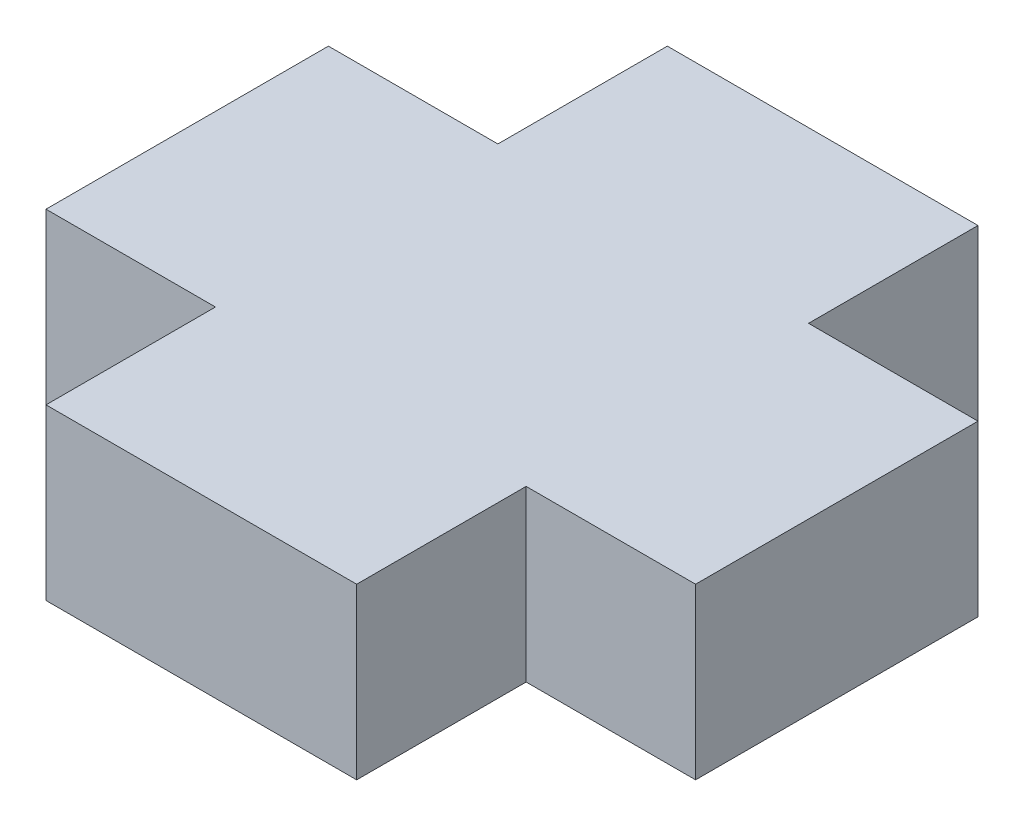
SolidWorks part; units mm, degrees
ref_plane "Front Plane" through (0, 0, 0) normal (0, 0, 1) x (1, 0, 0)
ref_plane "Top Plane" through (0, 0, 0) normal (0, 1, 0) x (1, 0, 0)
ref_plane "Right Plane" through (0, 0, 0) normal (1, 0, 0) x (0, 0, -1)
sketch "Sketch1" plane through (0, 0, 0) normal (0, 1, 0) x (1, 0, 0)
  line L0 (-16.2201, -4.3447) -> (-16.2201, 0.6553)
  line L1 (-16.2201, 0.6553) -> (-13.2201, 0.6553)
  line L2 (-13.2201, 0.6553) -> (-13.2201, 3.6553)
  line L3 (-13.2201, 3.6553) -> (-7.7201, 3.6553)
  line L4 (-7.7201, 3.6553) -> (-7.7201, 0.6553)
  line L5 (-7.7201, 0.6553) -> (-4.7201, 0.6553)
  line L6 (-4.7201, 0.6553) -> (-4.7201, -4.3447)
  line L7 (-4.7201, -4.3447) -> (-7.7201, -4.3447)
  line L8 (-7.7201, -4.3447) -> (-7.7201, -7.3447)
  line L9 (-7.7201, -7.3447) -> (-13.2201, -7.3447)
  line L10 (-13.2201, -7.3447) -> (-13.2201, -4.3447)
  line L11 (-13.2201, -4.3447) -> (-16.2201, -4.3447)
  dimension "D1" = 5
  dimension "D2" = 3
  dimension "D3" = 3
  dimension "D4" = 5.5
extrude "Boss-Extrude1" add sketch "Sketch1" along normal blind 3
